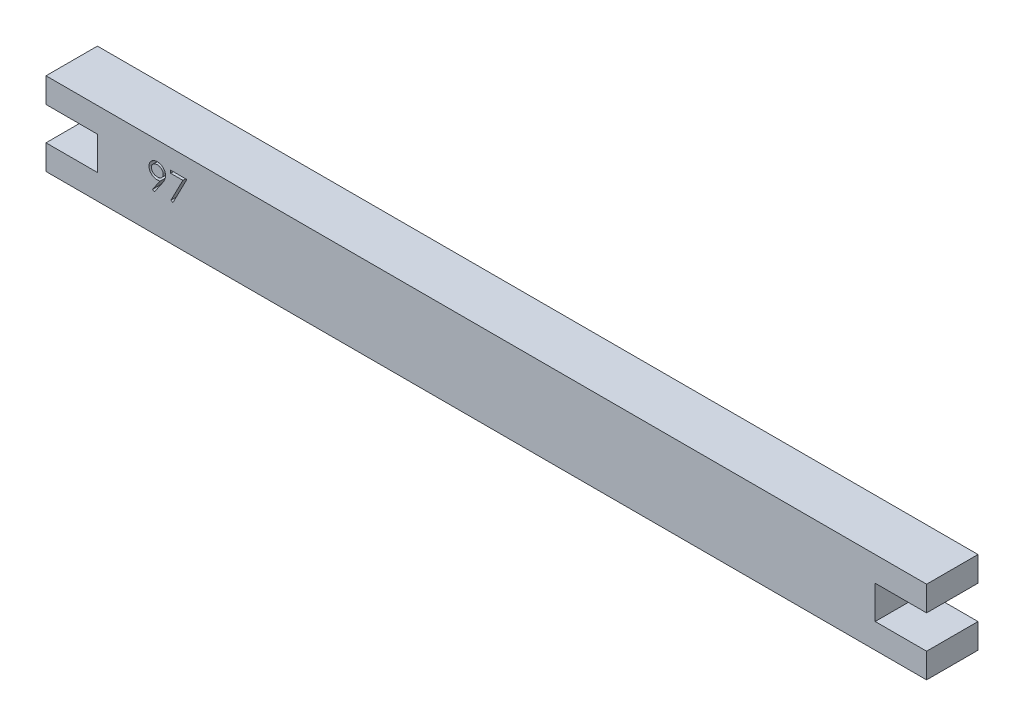
SolidWorks part; units mm, degrees
ref_plane "Front Plane" through (0, 0, 0) normal (0, 0, 1) x (1, 0, 0)
ref_plane "Top Plane" through (0, 0, 0) normal (0, 1, 0) x (1, 0, 0)
ref_plane "Right Plane" through (0, 0, 0) normal (1, 0, 0) x (0, 0, -1)
sketch "Sketch1" plane through (0, 0, 0) normal (0, 0, 1) x (1, 0, 0)
  line L3 (0, 7) -> (0, 3)
  line L4 (-6.2, 10) -> (100, 10)
  line L5 (100, 10) -> (100, 7)
  line L6 (100, 7) -> (93.8, 7)
  line L7 (93.8, 7) -> (93.8, 3)
  line L9 (93.8, 3) -> (100, 3)
  line L10 (100, 0) -> (100, 3)
  line L11 (-6.2, 0) -> (100, 0)
  line L13 (-6.2, 7) -> (-6.2, 10)
  line L14 (-6.2, 7) -> (0, 7)
  line L15 (0, 7) -> (0, 3)
  line L16 (0, 3) -> (-6.2, 3)
  line L17 (-6.2, 3) -> (-6.2, 0)
  dimension "D7" = 3
  dimension "D8" = 3
  dimension "D10" = 3
  dimension "D11" = 4
extrude "Boss-Extrude1" add sketch "Sketch1" along normal blind 6.2 contours L16 L17 L11 L10 L9 L7 L6 L5 L4 L13 L14 L3
sketch "Sketch2" plane through (0, 0, 6.2) normal (0, 0, 1) x (1, 0, 0)
  text T0 "97"
  point P1 (6.0612, 4.4838)
extrude "Cut-Extrude1" cut sketch "Sketch2" against normal blind 1
